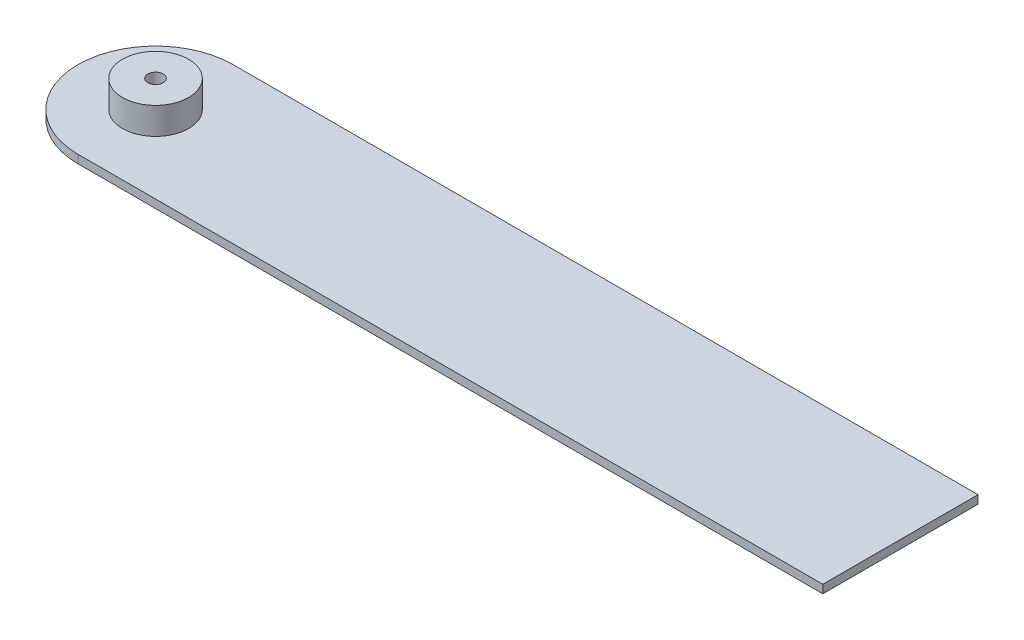
SolidWorks part; units mm, degrees
ref_plane "Front Plane" through (0, 0, 0) normal (0, 0, 1) x (1, 0, 0)
ref_plane "Top Plane" through (0, 0, 0) normal (0, 1, 0) x (1, 0, 0)
ref_plane "Right Plane" through (0, 0, 0) normal (1, 0, 0) x (0, 0, -1)
sketch "Sketch1" plane through (0, 0, 0) normal (0, 1, 0) x (1, 0, 0)
  line L1 (0, -7.5) -> (72, -7.5)
  line L2 (0, -7.5) -> (0, 7.5)
  line L3 (0, 7.5) -> (72, 7.5)
  line L4 (72, -7.5) -> (72, 7.5)
  circle A0 centre (0, 0) radius 7.5
  dimension "D1" = 15
  dimension "D2" = 72
  dimension "D3" = 15
extrude "Boss-Extrude1" add sketch "Sketch1" along normal blind 2 contours A0 L1 L4 L3 | L2 A0 | L2 A0
sketch "Sketch2" plane through (0, 2, 0) normal (0, 1, 0) x (1, 0, 0)
  circle A0 centre (0, 0) radius 0.74
extrude "Cut-Extrude1" cut sketch "Sketch2" against normal blind 5.6
sketch "Sketch4" plane through (0, 2, 0) normal (0, 1, 0) x (1, 0, 0)
  circle A0 centre (0, 0) radius 3.2
  circle A1 centre (0, 0) radius 0.74
sketch "Sketch6" plane through (0, 2, 0) normal (0, 1, 0) x (1, 0, 0)
  line L1 (72, 7.5) -> (-7.5, 7.5)
  line L2 (72, 7.5) -> (72, -7.5)
  line L3 (72, -7.5) -> (-7.5, -7.5)
  line L4 (-7.5, 7.5) -> (-7.5, -7.5)
  circle A0 centre (0, 0) radius 3.2
extrude "Cut-Extrude3" cut sketch "Sketch6" against normal blind 1.2
sketch "Sketch7" plane through (0, 2, 0) normal (0, 1, 0) x (1, 0, 0)
  circle A0 centre (0, 0) radius 0.74
  circle A1 centre (0, 0) radius 3.2
extrude "Boss-Extrude2" add sketch "Sketch7" along normal blind 1.4
sketch "Sketch8" plane through (0, 0, 0) normal (0, -1, 0) x (1, 0, 0)
  circle A0 centre (0, 0) radius 0.74
extrude "Boss-Extrude3" add sketch "Sketch8" against normal blind 0.4
